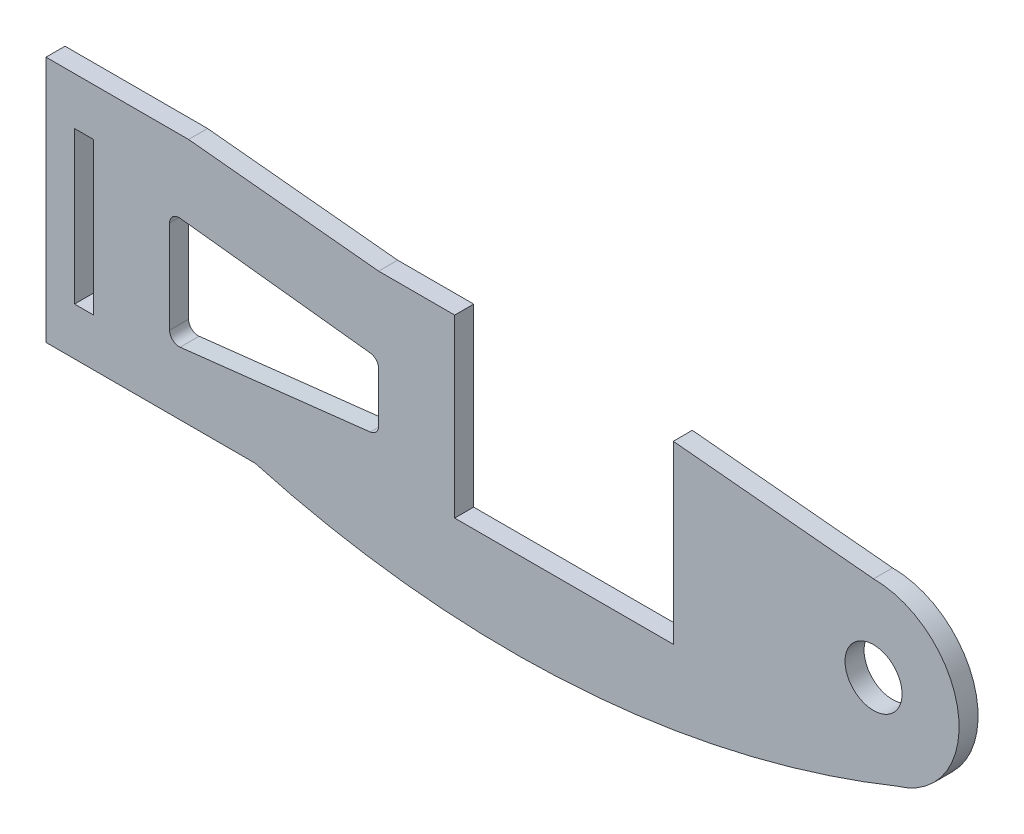
SolidWorks part; units mm, degrees
material "Plástico personalizado"
ref_plane "Plano frontal" through (0, 0, 0) normal (0, 0, 1) x (1, 0, 0)
ref_plane "Plano superior" through (0, 0, 0) normal (0, 1, 0) x (1, 0, 0)
ref_plane "Plano direito" through (0, 0, 0) normal (1, 0, 0) x (0, 0, -1)
sketch "Esboço1" plane through (0, 0, 0) normal (0, 0, 1) x (1, 0, 0)
  line L0 (-21.07, 11) -> (0, 9)
  line L1 (-21.07, 11) -> (-21.07, -7.5)
  line L2 (-21.07, -7.5) -> (-44.07, -7.5)
  line L3 (-44.07, -7.5) -> (-44.07, 11)
  line L4 (-72.07, 13) -> (-52.07, 11)
  line L5 (-87.07, 13) -> (-87.07, -13)
  line L6 (-87.07, -13) -> (-65.07, -13)
  line L7 (-87.07, 13) -> (-72.07, 13)
  line L8 (-52.07, 2.1072) -> (-52.07, -3.1072)
  line L9 (-52.9571, -4.1008) -> (-72.9571, -6.3735)
  line L10 (-52.07, 11) -> (-44.07, 11)
  line L11 (-74.07, -5.3799) -> (-74.07, 4.3799)
  line L12 (-72.9571, 5.3735) -> (-52.9571, 3.1008)
  line L14 (-84.07, -8) -> (-82.07, -8)
  line L15 (-84.07, -8) -> (-84.07, 8)
  line L16 (-84.07, 8) -> (-82.07, 8)
  line L17 (-82.07, -8) -> (-82.07, 8)
  line L18 (-84.07, -8) -> (-82.07, 8) construction
  line L19 (-84.07, 8) -> (-82.07, -8) construction
  arc A0 (2.4968, -8.6467) -> (0, 9) centre (0, 0) ccw
  circle A1 centre (0, 0) radius 3
  arc A2 (-52.9571, 3.1008) -> (-52.07, 2.1072) centre (-53.07, 2.1072) cw
  arc A3 (-52.07, -3.1072) -> (-52.9571, -4.1008) centre (-53.07, -3.1072) cw
  arc A4 (-74.07, -5.3799) -> (-72.9571, -6.3735) centre (-73.07, -5.3799) ccw
  arc A5 (-72.9571, 5.3735) -> (-74.07, 4.3799) centre (-73.07, 4.3799) ccw
  spline S0 degree 3 poles (-65.07, -13) (-43.2398, -19.0935) (-19.7501, -17.6424) (2.4968, -8.6467) knots 0 0 0 0 0.972963 0.972963 0.972963 0.972963
  point P21 (-52.07, 3)
  point P24 (-52.07, -4)
  point P27 (-74.07, -6.5)
  point P30 (-74.07, 5.5)
  point P31 (-83.07, 0)
  point P36 (-87.07, 0)
  point P37 (9, 0)
  dimension "D1" = 18
  dimension "D2" = 6
  dimension "D16" = 1
  dimension "D3" = 23
  dimension "D4" = 18.5
  dimension "D5" = 43
  dimension "D6" = 26
  dimension "D7" = 22
  dimension "D8" = 2
  dimension "D9" = 87.07
  dimension "D10" = 15
  dimension "D11" = 8
  dimension "D12" = 22
  dimension "D13" = 7
  dimension "D14" = 12
  dimension "D15" = 8
  dimension "D17" = 16
  dimension "D18" = 2
  dimension "D19" = 3
  dimension "D20" = 2
extrude "Ressalto-extrusão1" add sketch "Esboço1" along normal blind 2
